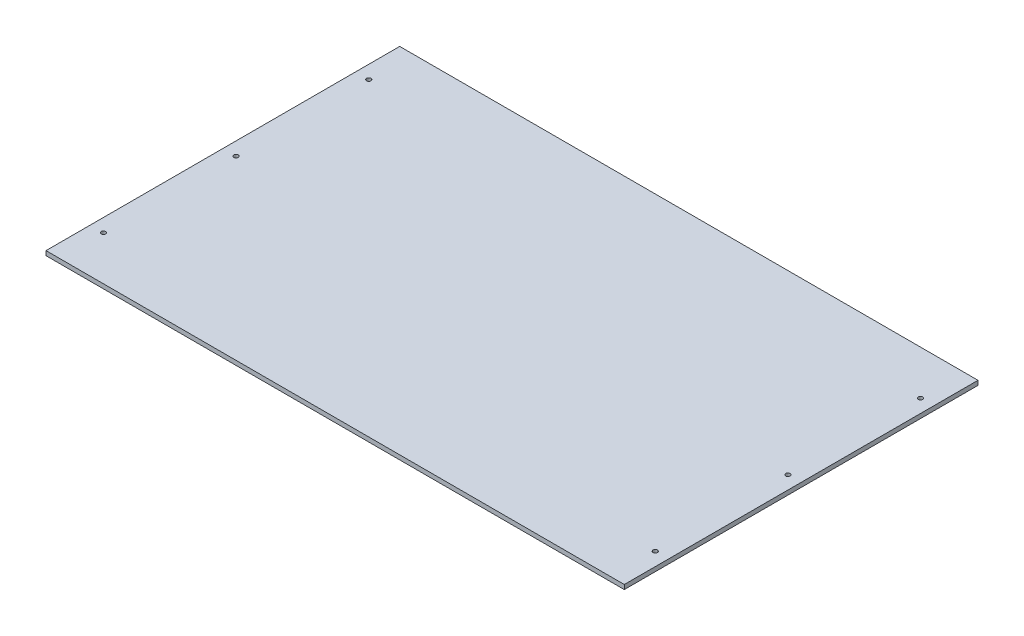
SolidWorks part; units mm, degrees
ref_plane "Front Plane" through (0, 0, 0) normal (0, 0, 1) x (1, 0, 0)
ref_plane "Top Plane" through (0, 0, 0) normal (0, 1, 0) x (1, 0, 0)
ref_plane "Right Plane" through (0, 0, 0) normal (1, 0, 0) x (0, 0, -1)
sketch "Sketch1" plane through (0, 0, 0) normal (0, 1, 0) x (1, 0, 0)
  line L1 (0, 0) -> (654, 0)
  line L2 (0, 0) -> (0, 400)
  line L3 (0, 400) -> (654, 400)
  line L4 (654, 0) -> (654, 400)
  dimension "D1" = 400
  dimension "D2" = 654
extrude "Boss-Extrude1" add sketch "Sketch1" along normal blind 5
sketch "Sketch2" plane through (0, 5, 0) normal (0, 1, 0) x (1, 0, 0)
  line L0 (0, 400) -> (0, 0) construction
  line L1 (654, 0) -> (654, 400) construction
  line L2 (654, 400) -> (0, 400) construction
  circle A0 centre (639, 350) radius 2.5
  circle A1 centre (639, 200) radius 2.5
  circle A2 centre (639, 50) radius 2.5
  circle A3 centre (15, 350) radius 2.5
  circle A4 centre (15, 200) radius 2.5
  circle A5 centre (15, 50) radius 2.5
  point P14 (0, 0)
  point P17 (0, 0)
  point P18 (0, 0)
  point P19 (0, 0)
  point P20 (0, 0)
  dimension "D1" = 5
  dimension "D2" = 15
  dimension "D3" = 15
  dimension "D4" = 150
  dimension "D5" = 150
  dimension "D6" = 50
extrude "Cut-Extrude1" cut sketch "Sketch2" against normal through all
